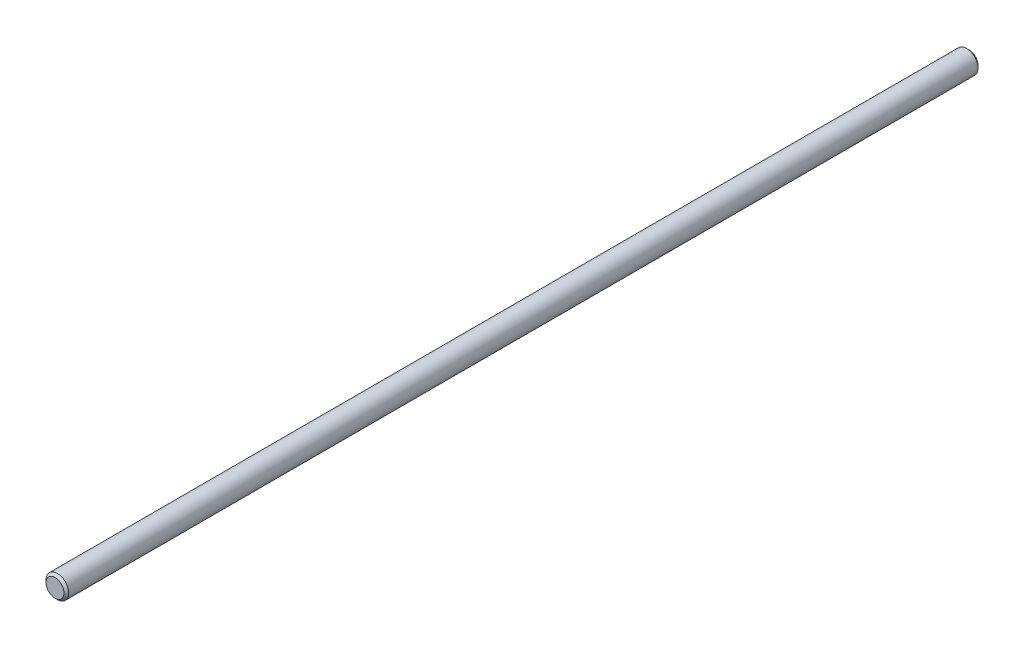
SolidWorks part; units mm, degrees
material "Chrome Stainless Steel"
ref_plane "Front Plane" through (0, 0, 0) normal (0, 0, 1) x (1, 0, 0)
ref_plane "Top Plane" through (0, 0, 0) normal (0, 1, 0) x (1, 0, 0)
ref_plane "Right Plane" through (0, 0, 0) normal (1, 0, 0) x (0, 0, -1)
sketch "Sketch1" plane through (0, 0, 0) normal (0, 0, 1) x (1, 0, 0)
  circle A0 centre (0, 0) radius 4.826
  dimension "D1" = 9.652
extrude "Boss-Extrude1" add sketch "Sketch1" along normal mid plane 389
chamfer "Chamfer1" distance 1 angle 45 2 edges at (4.826, 0, -194.5) (4.826, 0, 194.5)
sketch3d "3DSketch1"
  line L0 (0, 0, -194.5) -> (0, 0, 193.5) construction
  circle A0 centre (0, 0, 193.5) radius 4.826 construction
  circle A1 centre (0, 0, -194.5) radius 3.826 construction
  point P4 (0, 0, 188.674)
  point P7 (0, 0, -198.326)
